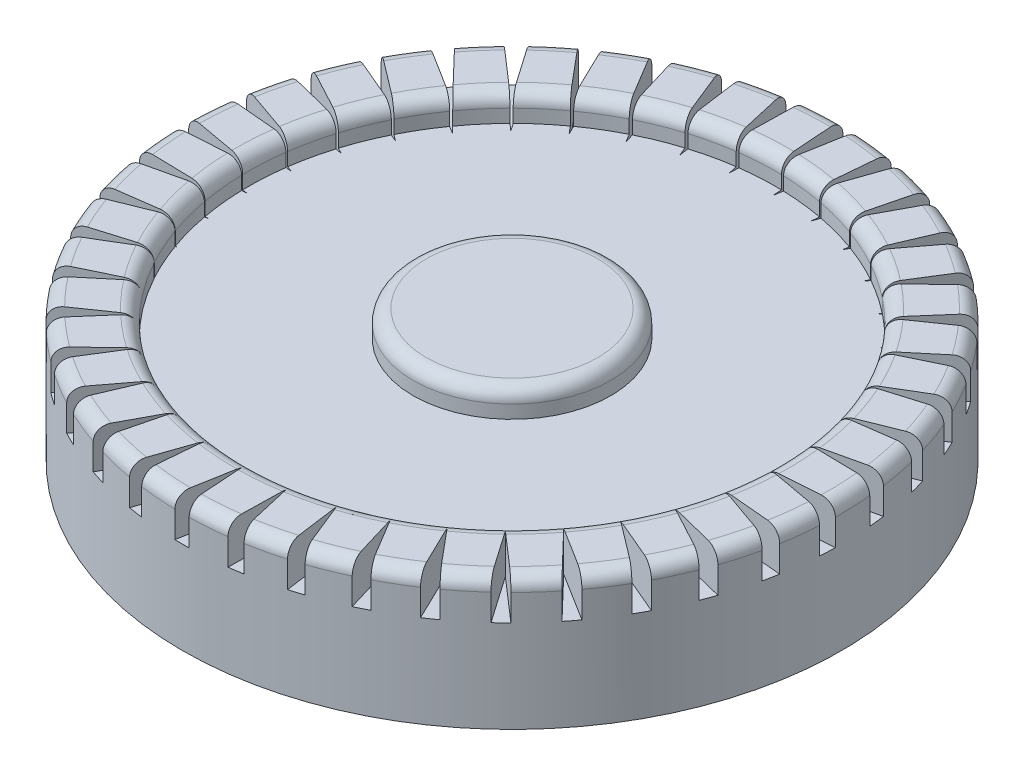
SolidWorks part; units mm, degrees
ref_plane "Front Plane" through (0, 0, 0) normal (0, 0, 1) x (1, 0, 0)
ref_plane "Top Plane" through (0, 0, 0) normal (0, 1, 0) x (1, 0, 0)
ref_plane "Right Plane" through (0, 0, 0) normal (1, 0, 0) x (0, 0, -1)
sketch "Sketch1" plane through (0, 0, 0) normal (0, 1, 0) x (1, 0, 0)
  circle A0 centre (-26.5743, 27.0394) radius 25
  dimension "D1" = 50
extrude "Boss-Extrude1" add sketch "Sketch1" along normal blind 10
sketch "Sketch2" plane through (0, 10, 0) normal (0, 1, 0) x (1, 0, 0)
  circle A0 centre (-26.5743, 27.0394) radius 20
  circle A1 centre (-26.5743, 27.0394) radius 7.5
  circle A2 centre (-26.5743, 27.0394) radius 25 construction
  dimension "D1" = 0
  dimension "D2" = 0
  dimension "D3" = 0
  dimension "D4" = 40
  dimension "D5" = 15
extrude "Cut-Extrude1" cut sketch "Sketch2" against normal blind 2
fillet "Fillet1" radius 1 3 edges at (-26.5743, 10, -2.0394) (-26.5743, 10, -7.0394) (-26.5743, 10, -19.5394)
sketch "Sketch3" plane through (0, 10, 0) normal (0, 1, 0) x (1, 0, 0)
  line L0 (-26.6192, 54.1496) -> (-26.0836, 46.3914)
  line L1 (-26.0836, 46.3914) -> (-24.6242, 54.4977)
  line L2 (-24.6242, 54.4977) -> (-26.6192, 54.1496)
  line L3 (-22.2729, 53.8688) -> (-22.9576, 46.1223)
  line L4 (-22.9576, 46.1223) -> (-20.248, 53.9005)
  line L5 (-20.248, 53.9005) -> (-22.2729, 53.8688)
  line L6 (-18.0241, 52.9115) -> (-19.9121, 45.3676)
  line L7 (-19.9121, 45.3676) -> (-16.0191, 52.6261)
  line L8 (-16.0191, 52.6261) -> (-18.0241, 52.9115)
  line L9 (-13.9773, 51.3014) -> (-17.0222, 44.1457)
  line L10 (-17.0222, 44.1457) -> (-12.0416, 50.7059)
  line L11 (-12.0416, 50.7059) -> (-13.9773, 51.3014)
  line L12 (-10.2321, 49.0781) -> (-14.359, 42.4868)
  line L13 (-14.359, 42.4868) -> (-8.4135, 48.187)
  line L14 (-8.4135, 48.187) -> (-10.2321, 49.0781)
  line L15 (-6.881, 46.2962) -> (-11.9881, 40.4316)
  line L16 (-11.9881, 40.4316) -> (-5.2241, 45.1317)
  line L17 (-5.2241, 45.1317) -> (-6.881, 46.2962)
  line L18 (-4.0062, 43.0244) -> (-9.9679, 38.0309)
  line L19 (-9.9679, 38.0309) -> (-2.5519, 41.615)
  line L20 (-2.5519, 41.615) -> (-4.0062, 43.0244)
  line L21 (-1.6787, 39.3431) -> (-8.3481, 35.3438)
  line L22 (-8.3481, 35.3438) -> (-0.4628, 37.7236)
  line L23 (-0.4628, 37.7236) -> (-1.6787, 39.3431)
  line L24 (0.0443, 35.3431) -> (-7.1686, 32.4363)
  line L25 (-7.1686, 32.4363) -> (0.9919, 33.5532)
  line L26 (0.9919, 33.5532) -> (0.0443, 35.3431)
  line L27 (1.1204, 31.1227) -> (-6.4585, 29.3801)
  line L28 (-6.4585, 29.3801) -> (1.7763, 29.2067)
  line L29 (1.7763, 29.2067) -> (1.1204, 31.1227)
  line L30 (1.523, 26.786) -> (-6.2352, 26.2504)
  line L31 (-6.2352, 26.2504) -> (1.8711, 24.791)
  line L32 (1.8711, 24.791) -> (1.523, 26.786)
  line L33 (1.2422, 22.4397) -> (-6.5043, 23.1244)
  line L34 (-6.5043, 23.1244) -> (1.2739, 20.4148)
  line L35 (1.2739, 20.4148) -> (1.2422, 22.4397)
  line L36 (0.285, 18.1908) -> (-7.259, 20.0789)
  line L37 (-7.259, 20.0789) -> (-0.0005, 16.1859)
  line L38 (-0.0005, 16.1859) -> (0.285, 18.1908)
  line L39 (-1.3252, 14.144) -> (-8.4809, 17.189)
  line L40 (-8.4809, 17.189) -> (-1.9207, 12.2084)
  line L41 (-1.9207, 12.2084) -> (-1.3252, 14.144)
  line L42 (-3.5485, 10.3989) -> (-10.1398, 14.5258)
  line L43 (-10.1398, 14.5258) -> (-4.4396, 8.5803)
  line L44 (-4.4396, 8.5803) -> (-3.5485, 10.3989)
  line L45 (-6.3304, 7.0477) -> (-12.195, 12.1549)
  line L46 (-12.195, 12.1549) -> (-7.4949, 5.3909)
  line L47 (-7.4949, 5.3909) -> (-6.3304, 7.0477)
  line L48 (-9.6022, 4.173) -> (-14.5957, 10.1347)
  line L49 (-14.5957, 10.1347) -> (-11.0116, 2.7187)
  line L50 (-11.0116, 2.7187) -> (-9.6022, 4.173)
  line L51 (-13.2835, 1.8454) -> (-17.2828, 8.5149)
  line L52 (-17.2828, 8.5149) -> (-14.903, 0.6296)
  line L53 (-14.903, 0.6296) -> (-13.2835, 1.8454)
  line L54 (-17.2835, 0.1224) -> (-20.1903, 7.3354)
  line L55 (-20.1903, 7.3354) -> (-19.0734, -0.8251)
  line L56 (-19.0734, -0.8251) -> (-17.2835, 0.1224)
  line L57 (-21.5039, -0.9536) -> (-23.2465, 6.6253)
  line L58 (-23.2465, 6.6253) -> (-23.4199, -1.6095)
  line L59 (-23.4199, -1.6095) -> (-21.5039, -0.9536)
  line L60 (-25.8406, -1.3562) -> (-26.3762, 6.402)
  line L61 (-26.3762, 6.402) -> (-27.8356, -1.7043)
  line L62 (-27.8356, -1.7043) -> (-25.8406, -1.3562)
  line L63 (-30.1869, -1.0754) -> (-29.5022, 6.671)
  line L64 (-29.5022, 6.671) -> (-32.2118, -1.1071)
  line L65 (-32.2118, -1.1071) -> (-30.1869, -1.0754)
  line L66 (-34.4357, -0.1182) -> (-32.5477, 7.4258)
  line L67 (-32.5477, 7.4258) -> (-36.4407, 0.1673)
  line L68 (-36.4407, 0.1673) -> (-34.4357, -0.1182)
  line L69 (-38.4826, 1.4919) -> (-35.4376, 8.6477)
  line L70 (-35.4376, 8.6477) -> (-40.4182, 2.0875)
  line L71 (-40.4182, 2.0875) -> (-38.4826, 1.4919)
  line L72 (-42.2277, 3.7153) -> (-38.1008, 10.3066)
  line L73 (-38.1008, 10.3066) -> (-44.0463, 4.6063)
  line L74 (-44.0463, 4.6063) -> (-42.2277, 3.7153)
  line L75 (-45.5789, 6.4971) -> (-40.4717, 12.3617)
  line L76 (-40.4717, 12.3617) -> (-47.2357, 7.6617)
  line L77 (-47.2357, 7.6617) -> (-45.5789, 6.4971)
  line L78 (-48.4536, 9.769) -> (-42.4919, 14.7624)
  line L79 (-42.4919, 14.7624) -> (-49.9079, 11.1784)
  line L80 (-49.9079, 11.1784) -> (-48.4536, 9.769)
  line L81 (-50.7811, 13.4503) -> (-44.1117, 17.4496)
  line L82 (-44.1117, 17.4496) -> (-51.997, 15.0698)
  line L83 (-51.997, 15.0698) -> (-50.7811, 13.4503)
  line L84 (-52.5041, 17.4503) -> (-45.2912, 20.3571)
  line L85 (-45.2912, 20.3571) -> (-53.4517, 19.2401)
  line L86 (-53.4517, 19.2401) -> (-52.5041, 17.4503)
  line L87 (-53.5802, 21.6706) -> (-46.0013, 23.4133)
  line L88 (-46.0013, 23.4133) -> (-54.2361, 23.5867)
  line L89 (-54.2361, 23.5867) -> (-53.5802, 21.6706)
  line L90 (-53.9828, 26.0074) -> (-46.2246, 26.543)
  line L91 (-46.2246, 26.543) -> (-54.3309, 28.0024)
  line L92 (-54.3309, 28.0024) -> (-53.9828, 26.0074)
  line L93 (-53.702, 30.3537) -> (-45.9555, 29.669)
  line L94 (-45.9555, 29.669) -> (-53.7337, 32.3786)
  line L95 (-53.7337, 32.3786) -> (-53.702, 30.3537)
  line L96 (-52.7448, 34.6025) -> (-45.2008, 32.7145)
  line L97 (-45.2008, 32.7145) -> (-52.4593, 36.6075)
  line L98 (-52.4593, 36.6075) -> (-52.7448, 34.6025)
  line L99 (-51.1346, 38.6493) -> (-43.9789, 35.6044)
  line L100 (-43.9789, 35.6044) -> (-50.5391, 40.585)
  line L101 (-50.5391, 40.585) -> (-51.1346, 38.6493)
  line L102 (-48.9113, 42.3944) -> (-42.32, 38.2676)
  line L103 (-42.32, 38.2676) -> (-48.0203, 44.2131)
  line L104 (-48.0203, 44.2131) -> (-48.9113, 42.3944)
  line L105 (-46.1294, 45.7456) -> (-40.2649, 40.6385)
  line L106 (-40.2649, 40.6385) -> (-44.9649, 47.4025)
  line L107 (-44.9649, 47.4025) -> (-46.1294, 45.7456)
  line L108 (-42.8576, 48.6204) -> (-37.8642, 42.6587)
  line L109 (-37.8642, 42.6587) -> (-41.4482, 50.0747)
  line L110 (-41.4482, 50.0747) -> (-42.8576, 48.6204)
  line L111 (-39.1763, 50.9479) -> (-35.177, 44.2785)
  line L112 (-35.177, 44.2785) -> (-37.5568, 52.1638)
  line L113 (-37.5568, 52.1638) -> (-39.1763, 50.9479)
  line L114 (-35.1763, 52.6709) -> (-32.2695, 45.458)
  line L115 (-32.2695, 45.458) -> (-33.3865, 53.6185)
  line L116 (-33.3865, 53.6185) -> (-35.1763, 52.6709)
  line L117 (-30.9559, 53.747) -> (-29.2133, 46.1681)
  line L118 (-29.2133, 46.1681) -> (-29.0399, 54.4029)
  line L119 (-29.0399, 54.4029) -> (-30.9559, 53.747)
  point P123 (-26.2299, 26.3967)
  dimension "D1" = 40
extrude "Cut-Extrude2" cut sketch "Sketch3" against normal blind 3
sketch "Sketch4" plane through (0, 0, 0) normal (0, -1, 0) x (1, 0, 0)
  circle A0 centre (-26.5743, -27.0394) radius 5
  circle A1 centre (-26.5743, -27.0394) radius 25 construction
  dimension "D1" = 0
  dimension "D2" = 10
extrude "Cut-Extrude3" cut sketch "Sketch4" against normal blind 0.1
